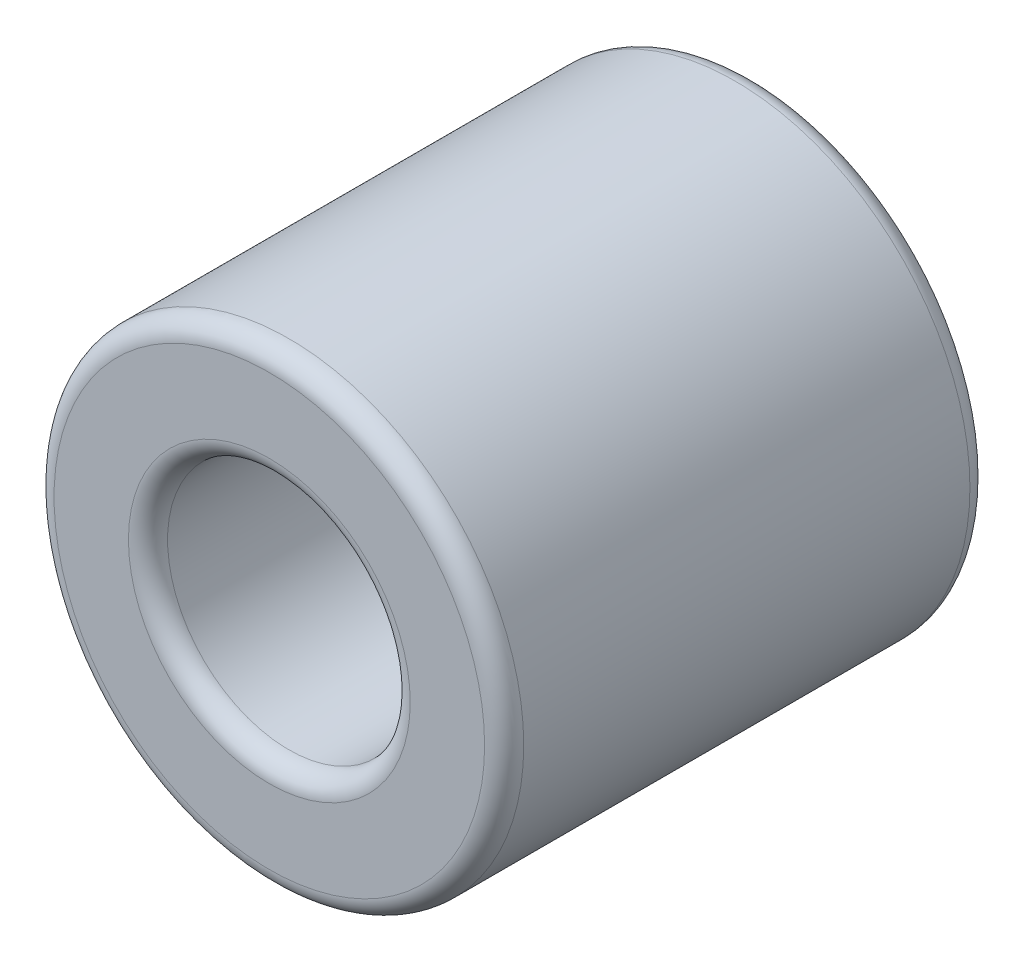
SolidWorks part; units mm, degrees
ref_plane "Přední rovina" through (0, 0, 0) normal (0, 0, 1) x (1, 0, 0)
ref_plane "Horní rovina" through (0, 0, 0) normal (0, 1, 0) x (1, 0, 0)
ref_plane "Pravá rovina" through (0, 0, 0) normal (1, 0, 0) x (0, 0, -1)
sketch "Skica2" plane through (0, 0, 0) normal (0, 0, 1) x (1, 0, 0)
  circle A0 centre (0, 0) radius 3
  circle A1 centre (0, 0) radius 1.55
  dimension "D1" = 6
  dimension "D2" = 3.1
extrude "Přidat vysunutím1" add sketch "Skica2" along normal blind 6.2
fillet "Zaoblit1" radius 0.25 4 edges at (1.55, 0, 0) (1.55, 0, 6.2) (3, 0, 0) (3, 0, 6.2)
